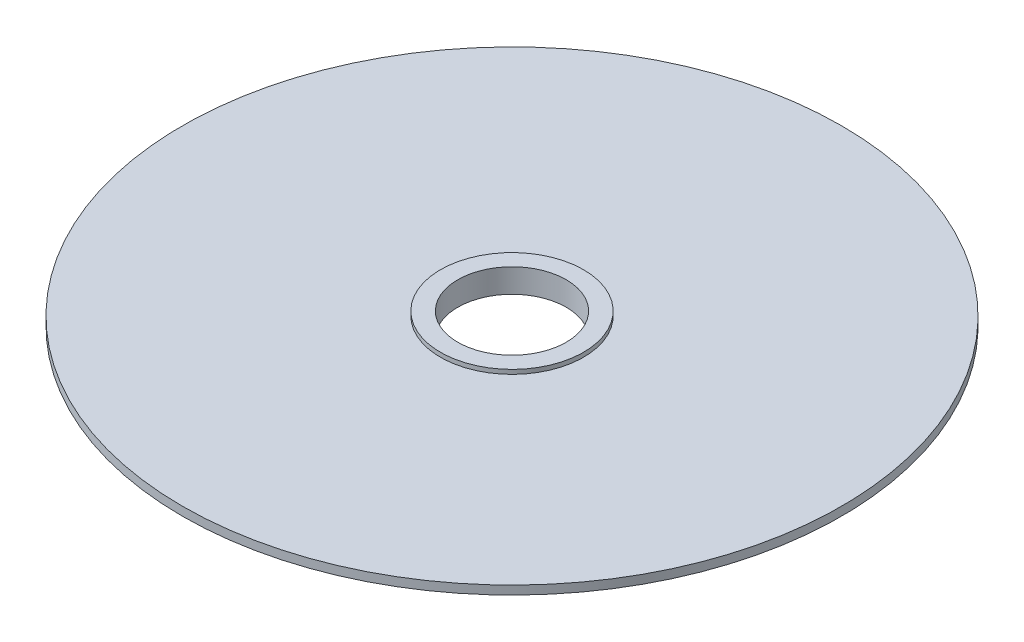
SolidWorks part; units mm, degrees
ref_plane "Alzado" through (0, 0, 0) normal (0, 0, 1) x (1, 0, 0)
ref_plane "Planta" through (0, 0, 0) normal (0, 1, 0) x (1, 0, 0)
ref_plane "Vista lateral" through (0, 0, 0) normal (1, 0, 0) x (0, 0, -1)
sketch "Sketch1" plane through (0, 0, 0) normal (0, 0, 1) x (1, 0, 0)
  line L0 (4, -1.6) -> (7.6, -1.6)
  line L1 (7.6, -1.6) -> (7.6, -1.4)
  line L2 (7.6, -1.4) -> (1.65, -1.4)
  line L3 (1.65, -1.4) -> (1.65, -1.3)
  line L4 (1.65, -1.3) -> (1.25, -1.3)
  line L5 (1.25, -1.3) -> (1.25, -1.85)
  line L6 (1.25, -1.85) -> (3.75, -1.85)
  line L7 (3.75, -1.85) -> (4, -1.6)
  line L8 (0, -1.3) -> (0, -1.85) construction
  dimension "D1" = 1.25
  dimension "D2" = 1.65
  dimension "D3" = 3.75
  dimension "D4" = 4
  dimension "D5" = 7.6
  dimension "D6" = 0.25
  dimension "D7" = 0.45
  dimension "D8" = 0.55
revolve "Revolve1" add sketch "Sketch1" angle 360 about L8
